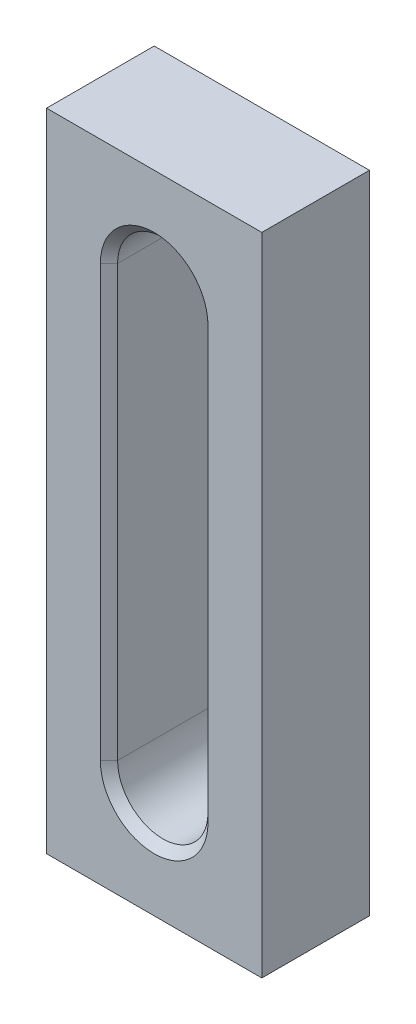
SolidWorks part; units mm, degrees
material "Простая углеродистая сталь"
ref_plane "Спереди" through (0, 0, 0) normal (0, 0, 1) x (1, 0, 0)
ref_plane "Сверху" through (0, 0, 0) normal (0, 1, 0) x (1, 0, 0)
ref_plane "Справа" through (0, 0, 0) normal (1, 0, 0) x (0, 0, -1)
sketch "Эскиз1" plane through (0, 0, 0) normal (0, 0, 1) x (1, 0, 0)
  line L1 (0, 0) -> (50, 0)
  line L2 (0, 0) -> (0, 150)
  line L3 (0, 150) -> (50, 150)
  line L4 (50, 0) -> (50, 150)
  dimension "D1" = 50
  dimension "D2" = 150
extrude "Бобышка-Вытянуть1" add sketch "Эскиз1" along normal blind 25
sketch "Эскиз2" plane through (0, 0, 25) normal (0, 0, 1) x (1, 0, 0)
  line L0 (35.5, 125) -> (35.5, 25)
  line L1 (14.5, 125) -> (14.5, 25)
  line L3 (0, 150) -> (0, 0) construction
  line L4 (0, 0) -> (50, 0) construction
  arc A0 (14.5, 25) -> (35.5, 25) centre (25, 25) ccw
  arc A1 (14.5, 125) -> (35.5, 125) centre (25, 125) cw
  dimension "D1" = 25
  dimension "D2" = 25
  dimension "D3" = 21
extrude "Вырез-Вытянуть1" cut sketch "Эскиз2" against normal through all
chamfer "Фаска1" distance 2 angle 45 8 edges at (14.5, 75, 0) (25, 14.5, 0) (25, 135.5, 0) (35.5, 75, 0) (35.5, 75, 25) (25, 135.5, 25) (25, 14.5, 25) (14.5, 75, 25)
